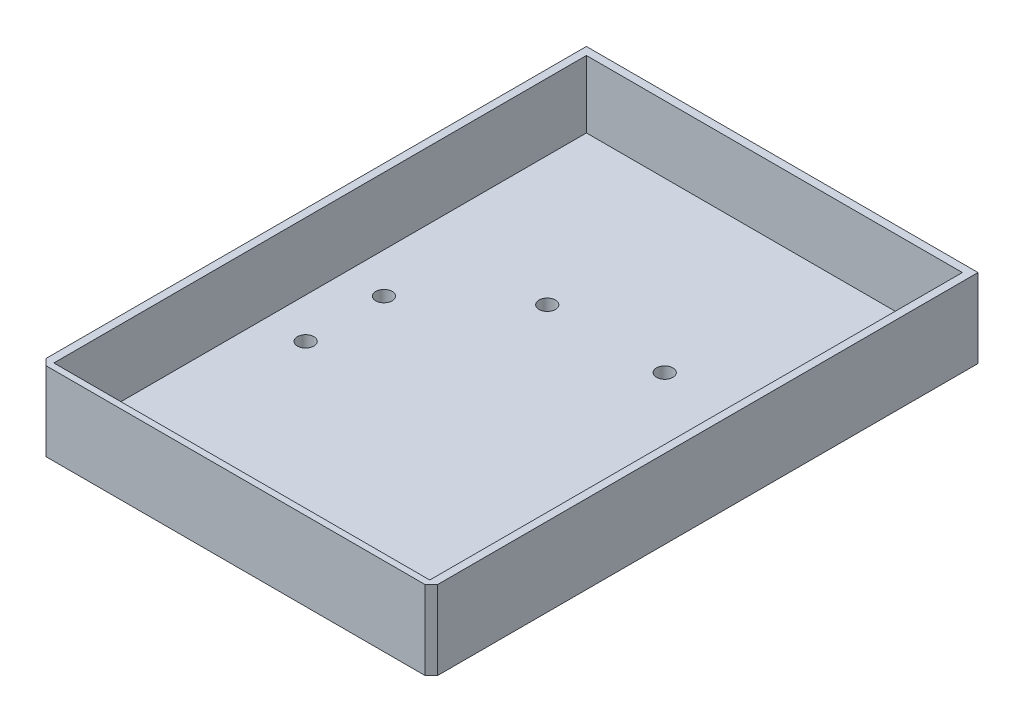
SolidWorks part; units mm, degrees
ref_plane "Front Plane" through (0, 0, 0) normal (0, 0, 1) x (1, 0, 0)
ref_plane "Top Plane" through (0, 0, 0) normal (0, 1, 0) x (1, 0, 0)
ref_plane "Right Plane" through (0, 0, 0) normal (1, 0, 0) x (0, 0, -1)
sketch "Sketch4" plane through (0, 0, 0) normal (0, 1, 0) x (1, 0, 0)
  line L3 (89.4442, -163.4248) -> (-10.5558, -163.4248)
  line L5 (89.4442, -63.4248) -> (-10.5558, -63.4248)
  line L6 (-10.5558, -163.4248) -> (-10.5558, -63.4248)
  line L7 (89.4442, -163.4248) -> (89.4442, -63.4248)
  circle A0 centre (1.6848, -87.3604) radius 2.1
  circle A1 centre (1.6848, -107.3604) radius 2.1
  circle A2 centre (1.6848, -152.3604) radius 2.1
  circle A3 centre (77.2035, -87.3604) radius 2.1
  circle A4 centre (77.2035, -107.3604) radius 2.1
  circle A5 centre (77.2035, -152.3604) radius 2.1
  circle A8 centre (54.4442, -158.4248) radius 2.1
  circle A9 centre (24.4442, -158.4248) radius 2.1
  circle A10 centre (54.4442, -68.4248) radius 2.1
  circle A11 centre (24.4442, -68.4248) radius 2.1
  dimension "D1" = 100
sketch "Sketch6" plane through (0, 0, 0) normal (0, 1, 0) x (1, 0, 0)
  line L0 (39.4442, -63.4248) -> (39.4442, -163.4248) construction
  line L1 (-10.5558, -63.4248) -> (89.4442, -63.4248)
  line L2 (-10.5558, -63.4248) -> (-10.5558, -163.4248)
  line L3 (-10.5558, -163.4248) -> (89.4442, -163.4248)
  line L4 (89.4442, -63.4248) -> (89.4442, -163.4248)
  circle A0 centre (1.6848, -87.3604) radius 2.1
  circle A1 centre (1.6848, -107.3604) radius 2.1
  circle A2 centre (1.6848, -152.3604) radius 2.1
  circle A3 centre (24.4442, -158.4248) radius 2.1
  circle A4 centre (24.4442, -68.4248) radius 2.1
  circle A5 centre (54.4442, -158.4248) radius 2.1
  circle A6 centre (77.2035, -152.3604) radius 2.1
  circle A7 centre (77.2035, -107.3604) radius 2.1
  circle A8 centre (77.2035, -87.3604) radius 2.1
  circle A9 centre (54.4442, -68.4248) radius 2.1
extrude "Boss-Extrude2" add sketch "Sketch6" along normal blind 3
sketch "Sketch7" plane through (0, 3, 0) normal (0, 1, 0) x (1, 0, 0)
  line L0 (89.4442, -63.4248) -> (-10.5558, -63.4248) construction
  line L1 (-10.5558, -163.4248) -> (-8.5558, -163.4248)
  line L2 (-10.5558, -163.4248) -> (-10.5558, -63.4248)
  line L3 (-10.5558, -63.4248) -> (-8.5558, -63.4248)
  line L4 (-8.5558, -163.4248) -> (-8.5558, -63.4248)
  line L5 (39.4442, -63.4248) -> (39.4442, -163.4248) construction
  line L6 (-10.5558, -163.4248) -> (89.4442, -163.4248) construction
  line L7 (89.4442, -63.4248) -> (87.4442, -63.4248)
  line L8 (87.4442, -163.4248) -> (87.4442, -63.4248)
  line L9 (89.4442, -163.4248) -> (87.4442, -163.4248)
  line L10 (89.4442, -163.4248) -> (89.4442, -63.4248)
  line L12 (-8.5558, -63.4248) -> (87.4442, -63.4248)
  line L13 (-8.5558, -63.4248) -> (-8.5558, -65.4248)
  line L14 (-8.5558, -65.4248) -> (87.4442, -65.4248)
  line L15 (87.4442, -63.4248) -> (87.4442, -65.4248)
  line M16 (-10.5558, -163.4248) -> (89.4442, -163.4248)
  line M17 (89.4442, -163.4248) -> (89.4442, -63.4248)
  line M18 (89.4442, -63.4248) -> (-10.5558, -63.4248)
  dimension "D1" = 2
  dimension "D2" = 0
  dimension "D3" = 2
extrude "Boss-Extrude3" add sketch "Sketch7" along normal blind 3 contours L5 L14 L8 M18 | L5 L12 L4 L14 | L8 M16 M17 M18
sketch "Sketch8" plane through (0, 3, 0) normal (0, 1, 0) x (1, 0, 0)
  line L0 (87.4442, -163.4248) -> (87.4442, -65.4248) construction
  line L1 (-8.5558, -163.4248) -> (87.4442, -163.4248)
  line L2 (-8.5558, -163.4248) -> (-8.5558, -161.4248)
  line L3 (-8.5558, -161.4248) -> (87.4442, -161.4248)
  line L4 (87.4442, -163.4248) -> (87.4442, -161.4248)
  dimension "D1" = 2
extrude "Boss-Extrude4" add sketch "Sketch8" along normal blind 3
chamfer "Chamfer1" distance 2 angle 45 4 edges at (-10.5558, 3, 63.4248) (-10.5558, 3, 163.4248) (89.4442, 3, 163.4248) (89.4442, 3, 63.4248)
sketch "Sketch9" plane through (0, 3, 0) normal (0, 1, 0) x (1, 0, 0)
  line L0 (-6.5558, -65.4248) -> (-8.5558, -67.4248)
  line L1 (-8.5558, -65.4248) -> (87.4442, -65.4248) construction
  line L2 (-8.5558, -161.4248) -> (-8.5558, -65.4248) construction
  line L3 (-8.5558, -67.4248) -> (-8.5558, -65.4248)
  line L4 (-8.5558, -65.4248) -> (-6.5558, -65.4248)
  line L5 (39.4442, -65.4248) -> (39.4442, -76.8168) construction
  line L6 (87.4442, -113.4248) -> (79.7492, -113.4248) construction
  line L7 (87.4442, -161.4248) -> (87.4442, -65.4248) construction
  line L8 (87.4442, -67.4248) -> (87.4442, -65.4248)
  line L9 (85.4442, -65.4248) -> (87.4442, -67.4248)
  line L10 (87.4442, -65.4248) -> (85.4442, -65.4248)
  line L11 (85.4442, -161.4248) -> (87.4442, -159.4248)
  line L12 (87.4442, -161.4248) -> (85.4442, -161.4248)
  line L13 (87.4442, -159.4248) -> (87.4442, -161.4248)
  line L14 (-8.5558, -159.4248) -> (-8.5558, -161.4248)
  line L15 (-6.5558, -161.4248) -> (-8.5558, -159.4248)
  line L16 (-8.5558, -161.4248) -> (-6.5558, -161.4248)
  dimension "D1" = 2
  dimension "D2" = 2
extrude "Boss-Extrude5" add sketch "Sketch9" along normal blind 3
sketch "Sketch10" plane through (-10.5558, 0, 0) normal (-1, 0, 0) x (0, 0, 1)
  line L1 (161.4248, 0) -> (63.4248, 0)
  line L2 (161.4248, 0) -> (161.4248, 25)
  line L3 (161.4248, 25) -> (63.4248, 25)
  line L4 (63.4248, 0) -> (63.4248, 25)
  dimension "D1" = 25
extrude "Boss-Extrude6" add sketch "Sketch10" against normal up to surface (2 mm away) contours L2 L1 L4 L3 up to face at (-8.5558, 4.5, 113.4248)
sketch "Sketch11" plane through (0, 0, 63.4248) normal (0, 0, -1) x (-1, 0, 0)
  line L1 (8.5558, 25) -> (10.5558, 25)
  line L2 (8.5558, 25) -> (8.5558, 0)
  line L3 (8.5558, 0) -> (10.5558, 0)
  line L4 (10.5558, 25) -> (10.5558, 0)
extrude "Boss-Extrude7" add sketch "Sketch11" along normal blind 40
sketch "Sketch12" plane through (89.4442, 0, 0) normal (1, 0, 0) x (0, 0, -1)
  line L1 (-161.4248, 25) -> (-23.4248, 25)
  line L2 (-161.4248, 25) -> (-161.4248, 0)
  line L3 (-161.4248, 0) -> (-23.4248, 0)
  line L4 (-23.4248, 25) -> (-23.4248, 0)
extrude "Boss-Extrude8" add sketch "Sketch12" against normal up to surface (2 mm away) up to face at (87.4442, 4.5, 113.4248)
sketch "Sketch13" plane through (0, 6, 0) normal (0, 1, 0) x (1, 0, 0)
  line L0 (-8.5558, -161.4248) -> (-6.5558, -161.4248)
  line L1 (-6.5558, -161.4248) -> (-8.5558, -159.4248)
  line L2 (-8.5558, -159.4248) -> (-8.5558, -161.4248)
  line L3 (85.4442, -161.4248) -> (87.4442, -161.4248)
  line L4 (87.4442, -161.4248) -> (87.4442, -159.4248)
  line L5 (87.4442, -159.4248) -> (85.4442, -161.4248)
extrude "Cut-Extrude1" cut sketch "Sketch13" against normal up to surface (3 mm away) contours L2 L0 L1 | L5 L3 L4 up to face at (77.2035, 3, 85.2604)
sketch "Sketch15" plane through (0, 6, 0) normal (0, 1, 0) x (1, 0, 0)
  line L0 (87.4442, -23.4248) -> (87.4442, -161.4248) construction
  line L1 (-8.5558, -63.4248) -> (87.4442, -63.4248)
  line L2 (-8.5558, -63.4248) -> (-8.5558, -69.7623)
  line L3 (-8.5558, -69.7623) -> (87.4442, -69.7623)
  line L4 (87.4442, -63.4248) -> (87.4442, -69.7623)
extrude "Cut-Extrude2" cut sketch "Sketch15" against normal up to surface (3 mm away) up to face at (77.2035, 3, 85.2604)
sketch "Sketch16" plane through (0, 0, 63.4248) normal (0, 0, -1) x (-1, 0, 0)
  line L1 (-87.4442, 3) -> (8.5558, 3)
  line L2 (-87.4442, 3) -> (-87.4442, 0)
  line L3 (-87.4442, 0) -> (8.5558, 0)
  line L4 (8.5558, 3) -> (8.5558, 0)
extrude "Boss-Extrude9" add sketch "Sketch16" along normal up to surface (40 mm away) up to face at (88.4442, 12.5, 23.4248)
sketch "Sketch17" plane through (0, 3, 0) normal (0, 1, 0) x (1, 0, 0)
  line L0 (87.4442, -23.4248) -> (87.4442, -161.4248) construction
  line L1 (-8.5558, -23.4248) -> (87.4442, -23.4248)
  line L2 (-8.5558, -23.4248) -> (-8.5558, -25.4248)
  line L3 (-8.5558, -25.4248) -> (87.4442, -25.4248)
  line L4 (87.4442, -23.4248) -> (87.4442, -25.4248)
  dimension "D1" = 2
extrude "Boss-Extrude10" add sketch "Sketch17" along normal up to surface (22 mm away) up to face at (-9.5558, 25, 92.4248)
sketch "Sketch18" plane through (0, 6, 0) normal (0, 1, 0) x (1, 0, 0)
  line L0 (-10.5558, -161.4248) -> (-8.5558, -163.4248)
  line L1 (-8.5558, -163.4248) -> (87.4442, -163.4248)
  line L2 (87.4442, -163.4248) -> (89.4442, -161.4248)
  line L3 (89.4442, -161.4248) -> (-10.5558, -161.4248)
extrude "Boss-Extrude11" add sketch "Sketch18" along normal up to surface (19 mm away) up to face at (39.4442, 25, 92.9248)
sketch "Sketch19" plane through (0, 0, 163.4248) normal (0, 0, 1) x (1, 0, 0)
  line L1 (-16.1859, 29.1587) -> (92.3419, 29.1587)
  line L2 (-16.1859, 29.1587) -> (-16.1859, -4.9407)
  line L3 (-16.1859, -4.9407) -> (92.3419, -4.9407)
  line L4 (92.3419, 29.1587) -> (92.3419, -4.9407)
extrude "Cut-Extrude3" cut sketch "Sketch19" against normal blind 0.4
sketch "Sketch20" plane through (0, 25, 0) normal (0, 1, 0) x (1, 0, 0)
  line L1 (-17.2823, -19.8732) -> (102.1731, -19.8732)
  line L2 (-17.2823, -19.8732) -> (-17.2823, -169.3407)
  line L3 (-17.2823, -169.3407) -> (102.1731, -169.3407)
  line L4 (102.1731, -19.8732) -> (102.1731, -169.3407)
extrude "Cut-Extrude4" cut sketch "Sketch20" against normal blind 4.87
